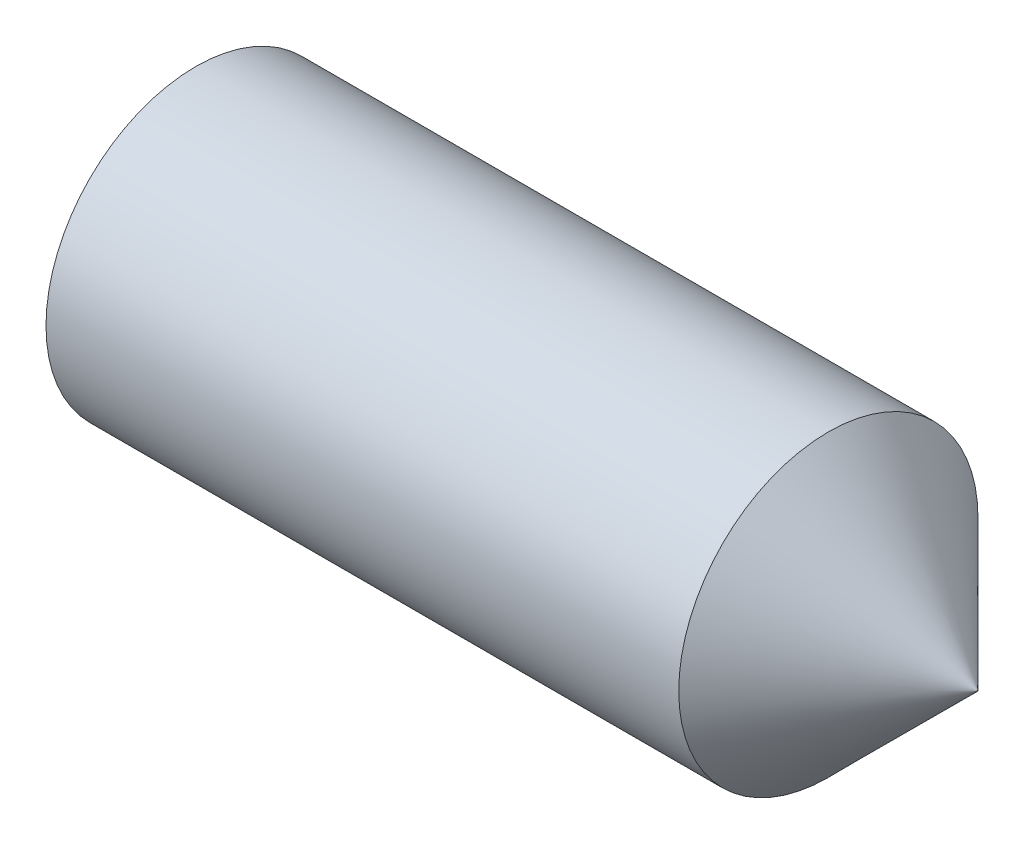
SolidWorks part; units mm, degrees
revolve "BaseBody" add sketch "BodySke" angle 360 about L5
sketch "BodySke" plane through (0, 0, 0) normal (0, 0, 1) x (1, 0, 0)
  line L0 (0, 0) -> (0, 1.2195)
  line L1 (0, 1.2195) -> (0.1619, 1.5)
  line L2 (0.1619, 1.5) -> (6.505, 1.5)
  line L3 (8, 0) -> (8, 0.005)
  line L4 (8, 0) -> (0, 0)
  line L5 (-12.7, 0) -> (88.9, 0) construction
  line L6 (8, 0.005) -> (6.505, 1.5)
  line L7 (0.5, 15.875) -> (0.5, -3.175) construction
  line L8 (0, -1.2195) -> (0.1619, -1.5) construction
  line L9 (8, -0.005) -> (6.505, -1.5) construction
  dimension "Diameter" = 3
  dimension "Drive_ch_ang" = 60
  dimension "Minor_dia" = 2.439
  dimension "Advance" = 0.5
  dimension "Length" = 8
  dimension "Tip_dia" = 0.01
  dimension "Cone_ang" = 90
cosmetic thread "ThreadCosmetic" parameters "Thread_minor"=2.439
ref_plane "Plane1" through (0, 0, 0) normal (0, 0, 1) x (1, 0, 0)
ref_plane "Plane2" through (0, 0, 0) normal (0, 1, 0) x (1, 0, 0)
ref_plane "Plane3" through (0, 0, 0) normal (1, 0, 0) x (0, 0, -1)
sketch "Sketch2" plane through (0, 0, 0) normal (-1, 0, 0) x (0, 0, 1)
  line L0 (0.433, 0.75) -> (-0.433, 0.75)
  line L1 (-0.433, 0.75) -> (-0.866, 0)
  line L2 (0.433, 0.75) -> (0.866, 0)
  line L3 (0.433, -0.75) -> (0.866, 0)
  line L4 (0.433, -0.75) -> (-0.433, -0.75)
  line L5 (-0.433, -0.75) -> (-0.866, 0)
  dimension "Hex_size" = 1.5
  dimension "D2" = 0.75
  dimension "D3" = 0.75
extrude "Hex" cut sketch "Sketch2" against normal blind 2.1
sketch "Sketch4" plane through (0, 4.7709, -0.5249) normal (-1, 0, 0) x (0, 0, 1)
  line L0 (0.5249, -4.7709) -> (1.3124, -4.7709)
  line L1 (0.5249, -4.7709) -> (6.6732, -1.2211) construction
  line L2 (0.5249, -4.7709) -> (0.9186, -4.0889)
  line L3 (1.153, -4.6137) -> (1.2782, -4.5415)
  line L4 (0.975, -4.3054) -> (1.1002, -4.2332)
  arc A0 (1.153, -4.6137) -> (0.975, -4.3054) centre (0.5249, -4.7709) ccw
  arc A1 (1.3124, -4.7709) -> (1.2782, -4.5415) centre (0.5249, -4.7709) ccw
  arc A2 (0.9186, -4.0889) -> (1.1002, -4.2332) centre (0.5249, -4.7709) cw
  circle A3 centre (0.5249, -4.7709) radius 0.6475 construction
  circle A4 centre (0.5249, -4.7709) radius 0.7875 construction
  dimension "Spline_n_dim" = 1.295
  dimension "Spline_m_dim" = 1.575
  dimension "D1" = 30
  dimension "Spline_a_dim" = 60
  dimension "Spline_p_dim" = 0.356
  dimension "D3" = 0.178
extrude "Spline6" [suppressed] cut sketch "Sketch4" against normal blind 1.2
pattern_circular "CirPattern1" [suppressed] count 6 every 60 about axis through (-12.7, 0, 0) along (1, 0, 0)
sketch "Sketch5" plane through (0, 1.4735, 6.925) normal (-1, 0, 0) x (0, 0, 1)
  line L0 (-6.925, -1.4735) -> (-6.1375, -1.4735)
  line L1 (-6.925, -1.4735) -> (-1.9049, 3.5466) construction
  line L2 (-6.925, -1.4735) -> (-6.925, -0.686)
  line L3 (-6.3413, -1.1415) -> (-6.2567, -1.0569)
  line L4 (-6.5931, -0.8898) -> (-6.5085, -0.8052)
  line L5 (-6.5931, -0.8898) -> (-6.3413, -1.1415)
  arc A1 (-6.1375, -1.4735) -> (-6.2567, -1.0569) centre (-6.925, -1.4735) ccw
  arc A2 (-6.925, -0.686) -> (-6.5085, -0.8052) centre (-6.925, -1.4735) cw
  circle A3 centre (-6.925, -1.4735) radius 0.6475 construction
  circle A4 centre (-6.925, -1.4735) radius 0.7875 construction
  dimension "Spline_n_dim" = 1.295
  dimension "Spline_m_dim" = 1.575
  dimension "Spline_p_dim" = 0.356
  dimension "D3" = 0.178
  dimension "D1" = 45
  dimension "Spline_a_dim" = 90
extrude "Spline4" [suppressed] cut sketch "Sketch5" against normal blind 1.2
pattern_circular "CirPattern2" [suppressed] count 4 every 90 about axis through (-12.7, 0, 0) along (1, 0, 0)
sketch "ThdSchSke" plane through (0, 0, 0) normal (0, 0, 1) x (1, 0, 0)
  line L0 (0.1619, -1.2195) -> (-0.0345, -1.5)
  line L1 (0.1619, -1.2195) -> (0.3584, -1.5)
  line L2 (0.3584, -1.5) -> (0.3584, -1.875)
  line L3 (-3.175, 0) -> (5.1513, 0) construction
  line L4 (0.1619, 1.5) -> (0.1619, -1.5) construction
  line L5 (0.3584, -1.875) -> (-0.0345, -1.875)
  line L6 (-0.0345, -1.875) -> (-0.0345, -1.5)
  dimension "Thread_minor" = 2.439
  dimension "Diameter" = 3
revolve "ThreadSchematic" [suppressed] cut sketch "ThdSchSke" angle 360 about L3
pattern_linear "ThdSchPat" [suppressed]
equation "\"D2@Sketch2\" = \"Hex_size@Sketch2\" / 2"
equation "\"D3@Sketch2\" = \"Hex_size@Sketch2\" / 2"
equation "\"Thread_minor@ThreadCosmetic\" = \"Minor_dia@BodySke\""
equation "\"D1@Sketch4\" = \"Spline_a_dim@Sketch4\" / 2"
equation "\"D3@Sketch4\" = \"Spline_p_dim@Sketch4\" / 2"
equation "\"D2@CirPattern1\" = \"Spline_a_dim@Sketch4\""
equation "\"Num_teeth@CirPattern1\" = 360 / \"D2@CirPattern1\""
equation "\"Spline_a_dim@Sketch5\" = 90"
equation "\"Spline_p_dim@Sketch5\" = \"Spline_p_dim@Sketch4\""
equation "\"Spline_m_dim@Sketch5\" = \"Spline_m_dim@Sketch4\""
equation "\"Spline_n_dim@Sketch5\" = \"Spline_n_dim@Sketch4\""
equation "\"D1@Sketch5\" = \"Spline_a_dim@Sketch5\" / 2"
equation "\"D3@Sketch5\" = \"Spline_p_dim@Sketch5\" / 2"
equation "\"Key_eng@Spline4\" = \"Key_eng@Spline6\""
equation "\"Thread_minor@ThdSchSke\" = \"Thread_minor@ThreadCosmetic\""
equation "\"Diameter@ThdSchSke\" = \"Diameter@BodySke\""
equation "\"Overcut@ThdSchSke\" = \"Diameter@BodySke\" * 1.25"
equation "\"Num_threads@ThdSchPat\" = int( (\"Length@BodySke\" - ( ( ( \"Diameter@BodySke\" - \"Minor_dia@BodySke\" ) * 0.5 ) / tan( \"Drive_ch_ang@BodySke\" * 0.017453292 ) ) - ( ( \"Diameter@BodySke\" * 0.5 ) / tan( \"Cone_ang@BodySke\" * 0.008726646 ) ) ) / \"Advance@BodySke\" + 0.999 )  + 1"
equation "\"Num_threads@ThdSchPat\" = int( (\"Length@BodySke\" - ( ( ( \"Diameter@BodySke\" - \"Minor_dia@BodySke\" ) * 0.5 ) / tan( \"Drive_ch_ang@BodySke\" * 0.017453292 ) ) - ( (( \"Diameter@BodySke\" - \"Tip_dia@BodySke\") * 0.5 ) / tan( \"Cone_ang@BodySke\" * 0.008726646 ) ) ) / \"Advance@BodySke\" + 0.999 )  + 1"
equation "\"Advance@ThdSchPat\" = (\"Length@BodySke\" - ( ( ( \"Diameter@BodySke\" - \"Minor_dia@BodySke\" ) * 0.5 ) / tan( \"Drive_ch_ang@BodySke\" * 0.017453292 ) ) - ( ( \"Diameter@BodySke\" * 0.5 ) / tan( \"Cone_ang@BodySke\" * 0.008726646 ) ) ) /  (\"Num_threads@ThdSchPat\" - 1) 'relax it"
equation "\"Advance@ThdSchPat\" = (\"Length@BodySke\" - ( ( ( \"Diameter@BodySke\" - \"Minor_dia@BodySke\" ) * 0.5 ) / tan( \"Drive_ch_ang@BodySke\" * 0.017453292 ) ) - ( ( (\"Diameter@BodySke\" - \"Tip_dia@BodySke\") * 0.5 ) / tan( \"Cone_ang@BodySke\" * 0.008726646 ) ) ) /  (\"Num_threads@ThdSchPat\" - 1) 'relax it"
equation "' \"Num_threads@ThdSchPat\" = \"Num_threads@ThdSchPat\" - sgn( \"Num_threads@ThdSchPat\" - 1) '---chamfered tips only---"
